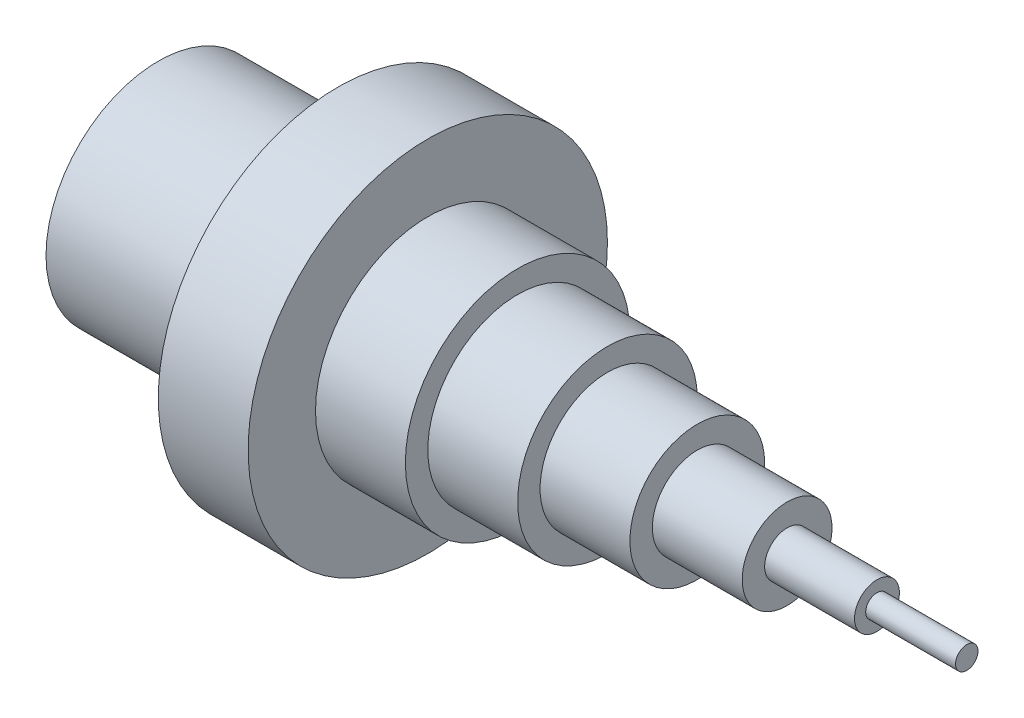
SolidWorks part; units mm, degrees
ref_plane "Front Plane" through (0, 0, 0) normal (0, 0, 1) x (1, 0, 0)
ref_plane "Top Plane" through (0, 0, 0) normal (0, 1, 0) x (1, 0, 0)
ref_plane "Right Plane" through (0, 0, 0) normal (1, 0, 0) x (0, 0, -1)
sketch "Sketch1" plane through (0, 0, 0) normal (0, 0, 1) x (1, 0, 0)
  line L0 (0, 0) -> (-180.3202, 0) construction
  line L1 (0, 0) -> (0, 2.5)
  line L2 (0, 2.5) -> (-20, 2.5)
  line L3 (-20, 2.5) -> (-20, 5)
  line L4 (-20, 5) -> (-40, 5)
  line L5 (-40, 5) -> (-40, 10)
  line L6 (-40, 10) -> (-60, 10)
  line L7 (-60, 10) -> (-60, 15)
  line L8 (-60, 15) -> (-80, 15)
  line L9 (-80, 15) -> (-80, 20)
  line L10 (-80, 20) -> (-100, 20)
  line L11 (-100, 20) -> (-100, 25)
  line L12 (-100, 25) -> (-120, 25)
  line L13 (-120, 25) -> (-120, 40)
  line L14 (-120, 40) -> (-140, 40)
  line L15 (-140, 40) -> (-140, 25)
  line L16 (-140, 25) -> (-180, 25)
  line L17 (-180, 25) -> (-180, 0)
  line L18 (-180.3202, 0) -> (0, 0)
  dimension "D1" = 20
  dimension "D2" = 40
  dimension "D3" = 5
  dimension "D4" = 10
  dimension "D5" = 20
  dimension "D6" = 30
  dimension "D7" = 40
  dimension "D8" = 50
  dimension "D9" = 80
  dimension "D10" = 50
  dimension "D11" = 180.3202
revolve "Revolve4" add sketch "Sketch1" angle 360 about L0
